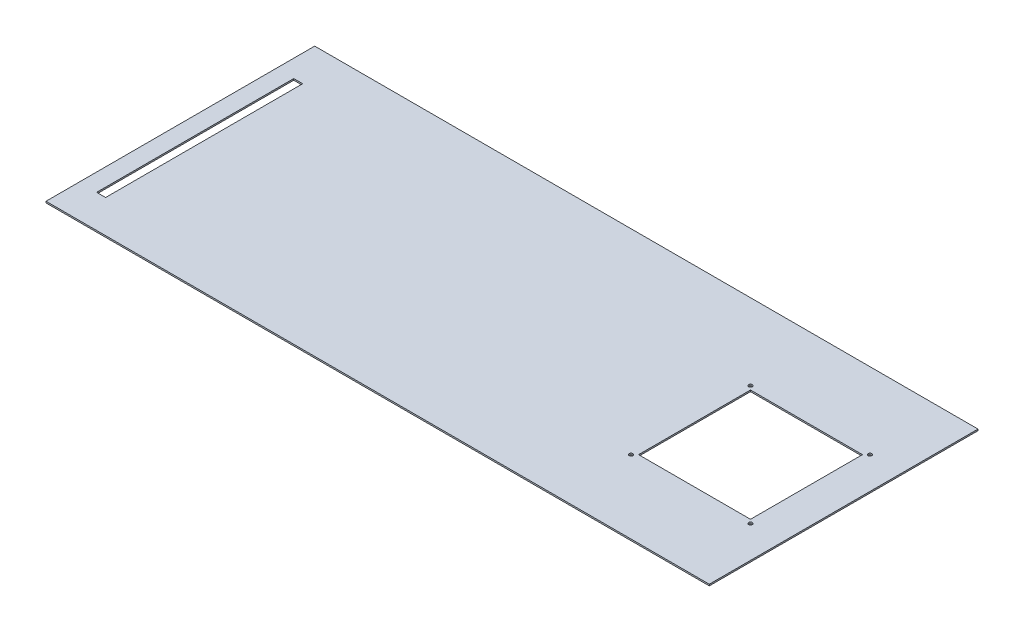
SolidWorks part; units mm, degrees
ref_plane "Front Plane" through (0, 0, 0) normal (0, 0, 1) x (1, 0, 0)
ref_plane "Top Plane" through (0, 0, 0) normal (0, 1, 0) x (1, 0, 0)
ref_plane "Right Plane" through (0, 0, 0) normal (1, 0, 0) x (0, 0, -1)
sketch "Sketch1" plane through (0, 0, 0) normal (0, 1, 0) x (1, 0, 0)
  line L1 (-462.9178, 190.9167) -> (425.7222, 190.9167)
  line L2 (-462.9178, 190.9167) -> (-462.9178, -169.0833)
  line L3 (-462.9178, -169.0833) -> (425.7222, -169.0833)
  line L4 (425.7222, 190.9167) -> (425.7222, -169.0833)
  dimension "D1" = 888.64
  dimension "D2" = 360
extrude "Boss-Extrude1" add sketch "Sketch1" along normal blind 2
sketch "Sketch2" plane through (0, 2, 0) normal (0, 1, 0) x (1, 0, 0)
  line L0 (425.7222, -169.0833) -> (425.7222, 190.9167) construction
  circle A0 centre (268.2222, 10.9167) radius 2.5
  point P4 (425.7222, 10.9167)
  dimension "D1" = 157.5
sketch "Sketch8" plane through (0, 2, 0) normal (0, 1, 0) x (1, 0, 0)
  line L1 (-439.3231, 139.2015) -> (-427.3231, 139.2015)
  line L2 (-439.3231, 139.2015) -> (-439.3231, -124.8368)
  line L3 (-439.3231, -124.8368) -> (-427.3231, -124.8368)
  line L4 (-427.3231, 139.2015) -> (-427.3231, -124.8368)
  dimension "D1" = 12
extrude "Cut-Extrude6" cut sketch "Sketch8" against normal blind 10
sketch "Sketch9" plane through (0, 2, 0) normal (0, 1, 0) x (1, 0, 0)
  line L0 (378.0185, 8.8387) -> (228.0185, 8.8387) construction
  line L1 (228.0185, 83.8387) -> (378.0185, 83.8387)
  line L2 (228.0185, 83.8387) -> (228.0185, -66.1613)
  line L3 (228.0185, -66.1613) -> (378.0185, -66.1613)
  line L4 (378.0185, 83.8387) -> (378.0185, -66.1613)
  line L5 (303.0185, 83.8387) -> (303.0185, -66.1613) construction
  circle A0 centre (223.0185, 88.8387) radius 2.5
  circle A1 centre (383.0185, 88.8387) radius 2.5
  circle A2 centre (383.0185, -71.1613) radius 2.5
  circle A3 centre (223.0185, -71.1613) radius 2.5
  dimension "D3" = 160
  dimension "D1" = 150
  dimension "D2" = 150
  dimension "D4" = 80
  dimension "D5" = 160
  dimension "D6" = 160
extrude "Cut-Extrude7" cut sketch "Sketch9" against normal blind 10
